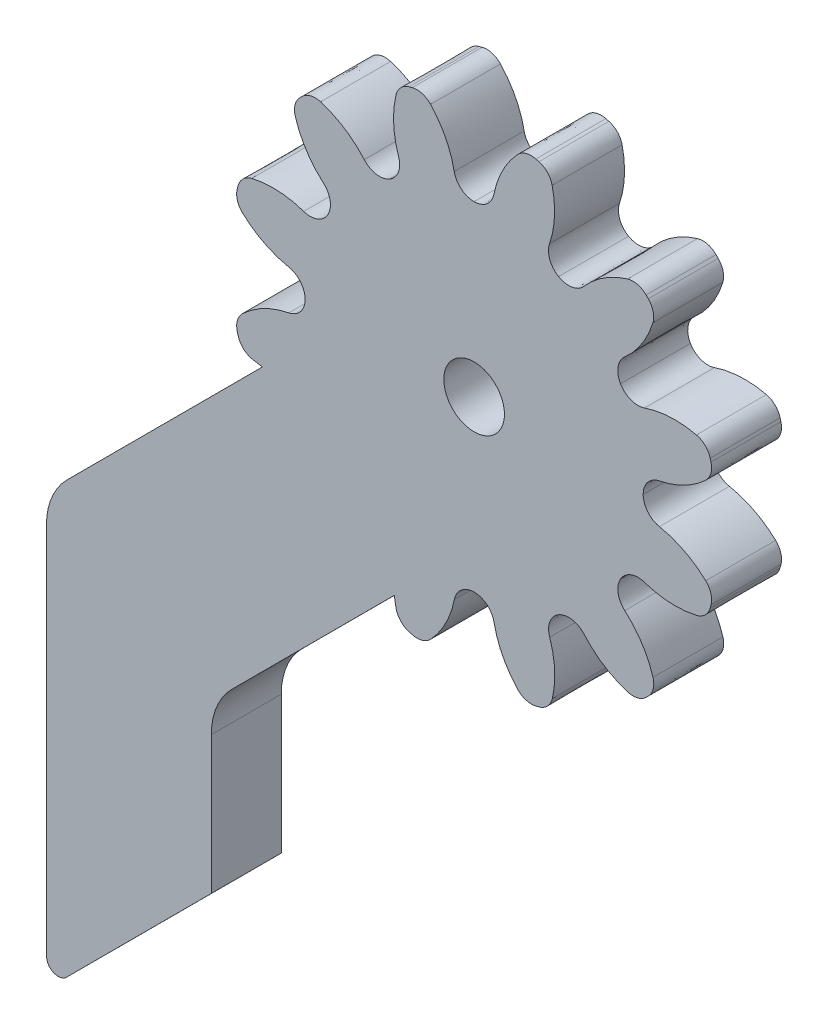
SolidWorks part; units mm, degrees
ref_plane "Front Plane" through (0, 0, 0) normal (0, 0, 1) x (1, 0, 0)
ref_plane "Top Plane" through (0, 0, 0) normal (0, 1, 0) x (1, 0, 0)
ref_plane "Right Plane" through (0, 0, 0) normal (1, 0, 0) x (0, 0, -1)
sketch "Model" plane through (0, 0, 0) normal (0, 0, 1) x (1, 0, 0)
  line L0 (37.1951, 19.5355) -> (37.1896, 26.0412)
  line L1 (44.264, 25.402) -> (38.0477, 19.1811)
  line L2 (46.4502, 46.0515) -> (38.0674, 37.6629)
  line L3 (45.14, 33.4228) -> (52.109, 40.3967)
  line L4 (44.2621, 31.3011) -> (44.264, 25.402)
  line L5 (37.1895, 35.5412) -> (37.1896, 26.0412)
  circle A0 centre (55.534, 49.4829) radius 1.3
  arc A2 (38.0674, 37.6629) -> (37.1895, 35.5412) centre (40.1895, 35.5424) ccw
  arc A3 (45.14, 33.4228) -> (44.2621, 31.3011) centre (47.2616, 31.3024) ccw
  arc A4 (37.1951, 19.5355) -> (38.0488, 19.1822) centre (37.6951, 19.5357) ccw
  spline S0 degree 3 poles (54.6867, 41.5337) (54.5406, 40.7904) (54.1887, 40.1031) (53.6712, 39.5501) knots 0 0 0 0 1 1 1 1
  spline S1 degree 3 poles (58.7749, 42.175) (59.0199, 41.4583) (59.0588, 40.6872) (58.8872, 39.9494) knots 0 0 0 0 1 1 1 1
  spline S2 degree 3 poles (61.9946, 44.7745) (62.5652, 44.2763) (62.9845, 43.628) (63.2047, 42.9032) knots 0 0 0 0 1 1 1 1
  spline S3 degree 3 poles (63.4833, 48.6356) (64.2264, 48.4895) (64.9137, 48.1376) (65.4669, 47.6201) knots 0 0 0 0 1 1 1 1
  spline S4 degree 3 poles (62.8419, 52.7238) (63.5586, 52.9689) (64.3298, 53.0077) (65.0675, 52.836) knots 0 0 0 0 1 1 1 1
  spline S5 degree 3 poles (60.2424, 55.9435) (60.7405, 56.5141) (61.3889, 56.9334) (62.1137, 57.1537) knots 0 0 0 0 1 1 1 1
  spline S6 degree 3 poles (56.3813, 57.4322) (56.5275, 58.1754) (56.8792, 58.8626) (57.3968, 59.4158) knots 0 0 0 0 1 1 1 1
  spline S7 degree 3 poles (52.2932, 56.7909) (52.0481, 57.5075) (52.0092, 58.2786) (52.1808, 59.0164) knots 0 0 0 0 1 1 1 1
  spline S8 degree 3 poles (49.0734, 54.1913) (48.5028, 54.6895) (48.0835, 55.3379) (47.8633, 56.0626) knots 0 0 0 0 1 1 1 1
  spline S9 degree 3 poles (47.5847, 50.3302) (46.8415, 50.4763) (46.1542, 50.8281) (45.6011, 51.3457) knots 0 0 0 0 1 1 1 1
  spline S10 degree 3 poles (46.4502, 46.0515) (46.2989, 46.0691) (46.1488, 46.0952) (46.0004, 46.1297) knots 0 0 0 0 1 1 1 1
  spline S11 degree 3 poles (54.6867, 41.5337) (54.7665, 41.9398) (55.1226, 42.2327) (55.5365, 42.2329) knots 0 0 0 0 0.333333 0.333333 0.333333 0.333333
  spline S12 degree 3 poles (55.5365, 42.2329) (55.9505, 42.233) (56.3067, 41.9403) (56.3869, 41.5342) knots 0.333333 0.333333 0.333333 0.333333 1 1 1 1
  spline S13 degree 3 poles (52.8852, 39.3225) (52.8417, 39.3338) (52.7982, 39.3455) (52.7548, 39.3574) knots 0 0 0 0 1 1 1 1
  spline S14 degree 3 poles (53.6712, 39.5501) (53.4708, 39.3358) (53.1691, 39.2484) (52.8852, 39.3225) knots 0 0 0 0 1 1 1 1
  spline S15 degree 3 poles (52.1874, 39.947) (52.1529, 40.0953) (52.1267, 40.2454) (52.109, 40.3967) knots 0 0 0 0 1 1 1 1
  spline S16 degree 3 poles (52.7548, 39.3574) (52.4719, 39.435) (52.2542, 39.6614) (52.1874, 39.947) knots 0 0 0 0 1 1 1 1
  spline S17 degree 3 poles (58.7749, 42.175) (58.6409, 42.5667) (58.8028, 42.9984) (59.1612, 43.2055) knots 0 0 0 0 0.333333 0.333333 0.333333 0.333333
  spline S18 degree 3 poles (59.1612, 43.2055) (59.5197, 43.4126) (59.9745, 43.3372) (60.247, 43.0256) knots 0.333333 0.333333 0.333333 0.333333 1 1 1 1
  spline S19 degree 3 poles (58.3203, 39.3593) (58.2769, 39.3474) (58.2334, 39.3357) (58.1899, 39.3244) knots 0 0 0 0 1 1 1 1
  spline S20 degree 3 poles (58.8872, 39.9494) (58.8207, 39.6636) (58.6032, 39.4372) (58.3203, 39.3593) knots 0 0 0 0 1 1 1 1
  spline S21 degree 3 poles (57.4037, 39.5513) (56.8858, 40.1041) (56.5335, 40.7911) (56.3869, 41.5342) knots 0 0 0 0 1 1 1 1
  spline S22 degree 3 poles (58.1899, 39.3244) (57.9061, 39.2501) (57.6043, 39.3372) (57.4037, 39.5513) knots 0 0 0 0 1 1 1 1
  spline S23 degree 3 poles (61.9946, 44.7745) (61.6828, 45.0467) (61.6071, 45.5015) (61.814, 45.8602) knots 0 0 0 0 0.333333 0.333333 0.333333 0.333333
  spline S24 degree 3 poles (61.814, 45.8602) (62.0208, 46.2187) (62.4524, 46.3809) (62.8442, 46.2472) knots 0.333333 0.333333 0.333333 0.333333 1 1 1 1
  spline S25 degree 3 poles (63.0088, 42.1088) (62.9772, 42.0767) (62.9454, 42.0449) (62.9134, 42.0133) knots 0 0 0 0 1 1 1 1
  spline S26 degree 3 poles (63.2047, 42.9032) (63.29, 42.6225) (63.2149, 42.3177) (63.0088, 42.1088) knots 0 0 0 0 1 1 1 1
  spline S27 degree 3 poles (62.1191, 41.8168) (61.3942, 42.0365) (60.7456, 42.4554) (60.247, 43.0256) knots 0 0 0 0 1 1 1 1
  spline S28 degree 3 poles (62.9134, 42.0133) (62.7047, 41.807) (62.3998, 41.7317) (62.1191, 41.8168) knots 0 0 0 0 1 1 1 1
  spline S29 degree 3 poles (63.4833, 48.6356) (63.0771, 48.7155) (62.7841, 49.0715) (62.7841, 49.4855) knots 0 0 0 0 0.333333 0.333333 0.333333 0.333333
  spline S30 degree 3 poles (62.7841, 49.4855) (62.7839, 49.8995) (63.0765, 50.2556) (63.4827, 50.3358) knots 0.333333 0.333333 0.333333 0.333333 1 1 1 1
  spline S31 degree 3 poles (65.6944, 46.8341) (65.683, 46.7906) (65.6714, 46.7471) (65.6595, 46.7037) knots 0 0 0 0 1 1 1 1
  spline S32 degree 3 poles (65.4669, 47.6201) (65.6811, 47.4196) (65.7684, 47.118) (65.6944, 46.8341) knots 0 0 0 0 1 1 1 1
  spline S33 degree 3 poles (65.0698, 46.1363) (64.3322, 45.9643) (63.5611, 46.0026) (62.8442, 46.2472) knots 0 0 0 0 1 1 1 1
  spline S34 degree 3 poles (65.6595, 46.7037) (65.5818, 46.4208) (65.3556, 46.203) (65.0698, 46.1363) knots 0 0 0 0 1 1 1 1
  spline S35 degree 3 poles (62.8419, 52.7238) (62.4502, 52.5899) (62.0185, 52.7517) (61.8115, 53.1101) knots 0 0 0 0 0.333333 0.333333 0.333333 0.333333
  spline S36 degree 3 poles (61.8115, 53.1101) (61.6043, 53.4685) (61.6797, 53.9233) (61.9913, 54.1958) knots 0.333333 0.333333 0.333333 0.333333 1 1 1 1
  spline S37 degree 3 poles (65.6575, 52.2692) (65.6695, 52.2258) (65.6812, 52.1823) (65.6926, 52.1388) knots 0 0 0 0 1 1 1 1
  spline S38 degree 3 poles (65.0675, 52.836) (65.3532, 52.7696) (65.5797, 52.5521) (65.6575, 52.2692) knots 0 0 0 0 1 1 1 1
  spline S39 degree 3 poles (65.4655, 51.3526) (64.9128, 50.8347) (64.2258, 50.4824) (63.4827, 50.3358) knots 0 0 0 0 1 1 1 1
  spline S40 degree 3 poles (65.6926, 52.1388) (65.7668, 51.855) (65.6796, 51.5532) (65.4655, 51.3526) knots 0 0 0 0 1 1 1 1
  spline S41 degree 3 poles (60.2424, 55.9435) (59.9701, 55.6317) (59.5153, 55.556) (59.1568, 55.7629) knots 0 0 0 0 0.333333 0.333333 0.333333 0.333333
  spline S42 degree 3 poles (59.1568, 55.7629) (58.7982, 55.9697) (58.636, 56.4013) (58.7697, 56.7931) knots 0.333333 0.333333 0.333333 0.333333 1 1 1 1
  spline S43 degree 3 poles (62.9081, 56.9577) (62.9401, 56.926) (62.972, 56.8943) (63.0037, 56.8622) knots 0 0 0 0 1 1 1 1
  spline S44 degree 3 poles (62.1137, 57.1537) (62.3944, 57.239) (62.6992, 57.1637) (62.9081, 56.9577) knots 0 0 0 0 1 1 1 1
  spline S45 degree 3 poles (63.2001, 56.0679) (62.9804, 55.3431) (62.5616, 54.6944) (61.9913, 54.1958) knots 0 0 0 0 1 1 1 1
  spline S46 degree 3 poles (63.0037, 56.8622) (63.2098, 56.6535) (63.2852, 56.3487) (63.2001, 56.0679) knots 0 0 0 0 1 1 1 1
  spline S47 degree 3 poles (56.3813, 57.4322) (56.3014, 57.026) (55.9454, 56.733) (55.5314, 56.7329) knots 0 0 0 0 0.333333 0.333333 0.333333 0.333333
  spline S48 degree 3 poles (55.5314, 56.7329) (55.1175, 56.7327) (54.7612, 57.0254) (54.6811, 57.4316) knots 0.333333 0.333333 0.333333 0.333333 1 1 1 1
  spline S49 degree 3 poles (58.1828, 59.6433) (58.2263, 59.632) (58.2698, 59.6203) (58.3132, 59.6085) knots 0 0 0 0 1 1 1 1
  spline S50 degree 3 poles (57.3968, 59.4158) (57.5972, 59.63) (57.8989, 59.7173) (58.1828, 59.6433) knots 0 0 0 0 1 1 1 1
  spline S51 degree 3 poles (58.8805, 59.0187) (59.0527, 58.2812) (59.0143, 57.51) (58.7697, 56.7931) knots 0 0 0 0 1 1 1 1
  spline S52 degree 3 poles (58.3132, 59.6085) (58.5961, 59.5307) (58.8139, 59.3045) (58.8805, 59.0187) knots 0 0 0 0 1 1 1 1
  spline S53 degree 3 poles (52.2932, 56.7909) (52.427, 56.3991) (52.2652, 55.9674) (51.9068, 55.7603) knots 0 0 0 0 0.333333 0.333333 0.333333 0.333333
  spline S54 degree 3 poles (51.9068, 55.7603) (51.5484, 55.5532) (51.0935, 55.6285) (50.8211, 55.9403) knots 0.333333 0.333333 0.333333 0.333333 1 1 1 1
  spline S55 degree 3 poles (52.7477, 59.6065) (52.7911, 59.6184) (52.8345, 59.6301) (52.8781, 59.6414) knots 0 0 0 0 1 1 1 1
  spline S56 degree 3 poles (52.1808, 59.0164) (52.2473, 59.3021) (52.4648, 59.5286) (52.7477, 59.6065) knots 0 0 0 0 1 1 1 1
  spline S57 degree 3 poles (53.6642, 59.4144) (54.1821, 58.8617) (54.5344, 58.1747) (54.6811, 57.4316) knots 0 0 0 0 1 1 1 1
  spline S58 degree 3 poles (52.8781, 59.6414) (53.1619, 59.7157) (53.4636, 59.6285) (53.6642, 59.4144) knots 0 0 0 0 1 1 1 1
  spline S59 degree 3 poles (49.0734, 54.1913) (49.3853, 53.9191) (49.4609, 53.4642) (49.254, 53.1058) knots 0 0 0 0 0.333333 0.333333 0.333333 0.333333
  spline S60 degree 3 poles (49.254, 53.1058) (49.0472, 52.7471) (48.6156, 52.585) (48.2238, 52.7186) knots 0.333333 0.333333 0.333333 0.333333 1 1 1 1
  spline S61 degree 3 poles (48.0592, 56.857) (48.0908, 56.889) (48.1227, 56.9209) (48.1546, 56.9526) knots 0 0 0 0 1 1 1 1
  spline S62 degree 3 poles (47.8633, 56.0626) (47.778, 56.3434) (47.8532, 56.6482) (48.0592, 56.857) knots 0 0 0 0 1 1 1 1
  spline S63 degree 3 poles (48.949, 57.149) (49.6738, 56.9293) (50.3225, 56.5105) (50.8211, 55.9403) knots 0 0 0 0 1 1 1 1
  spline S64 degree 3 poles (48.1546, 56.9526) (48.3633, 57.1587) (48.6681, 57.2341) (48.949, 57.149) knots 0 0 0 0 1 1 1 1
  spline S65 degree 3 poles (47.5847, 50.3302) (47.9909, 50.2503) (48.2839, 49.8943) (48.284, 49.4804) knots 0 0 0 0 0.333333 0.333333 0.333333 0.333333
  spline S66 degree 3 poles (48.284, 49.4804) (48.2841, 49.0664) (47.9915, 48.7102) (47.5853, 48.6301) knots 0.333333 0.333333 0.333333 0.333333 1 1 1 1
  spline S67 degree 3 poles (45.3736, 52.1316) (45.3849, 52.1752) (45.3966, 52.2187) (45.4085, 52.2621) knots 0 0 0 0 1 1 1 1
  spline S68 degree 3 poles (45.6011, 51.3457) (45.3868, 51.5461) (45.2995, 51.8477) (45.3736, 52.1316) knots 0 0 0 0 1 1 1 1
  spline S69 degree 3 poles (45.9981, 52.8294) (46.7358, 53.0015) (47.5069, 52.9632) (48.2238, 52.7186) knots 0 0 0 0 1 1 1 1
  spline S70 degree 3 poles (45.4085, 52.2621) (45.4861, 52.545) (45.7124, 52.7627) (45.9981, 52.8294) knots 0 0 0 0 1 1 1 1
  spline S71 degree 3 poles (45.4104, 46.6965) (45.3984, 46.74) (45.3869, 46.7835) (45.3754, 46.827) knots 0 0 0 0 1 1 1 1
  spline S72 degree 3 poles (46.0004, 46.1297) (45.7147, 46.1961) (45.4883, 46.4137) (45.4104, 46.6965) knots 0 0 0 0 1 1 1 1
  spline S73 degree 3 poles (45.6024, 47.6131) (46.1552, 48.131) (46.8422, 48.4833) (47.5853, 48.6301) knots 0 0 0 0 1 1 1 1
  spline S74 degree 3 poles (45.3754, 46.827) (45.3013, 47.1109) (45.3883, 47.4125) (45.6024, 47.6131) knots 0 0 0 0 1 1 1 1
extrude "Boss-Extrude1" add sketch "Model" along normal blind 3 contours S74 S71 S72 S10 L2 A2 L5 L0 A4 L1 L4 A3 L3 S15 S16 S13 S14 S0 S11 S12 S21 S22 S19 S20 S1 S17 S18 S27 S28 S25 S26 S2 S23 S24 S33 S34 S31 S32 S3 S29 S30 S39 S40 S37 S38 S4 S35 S36 S45 S46
